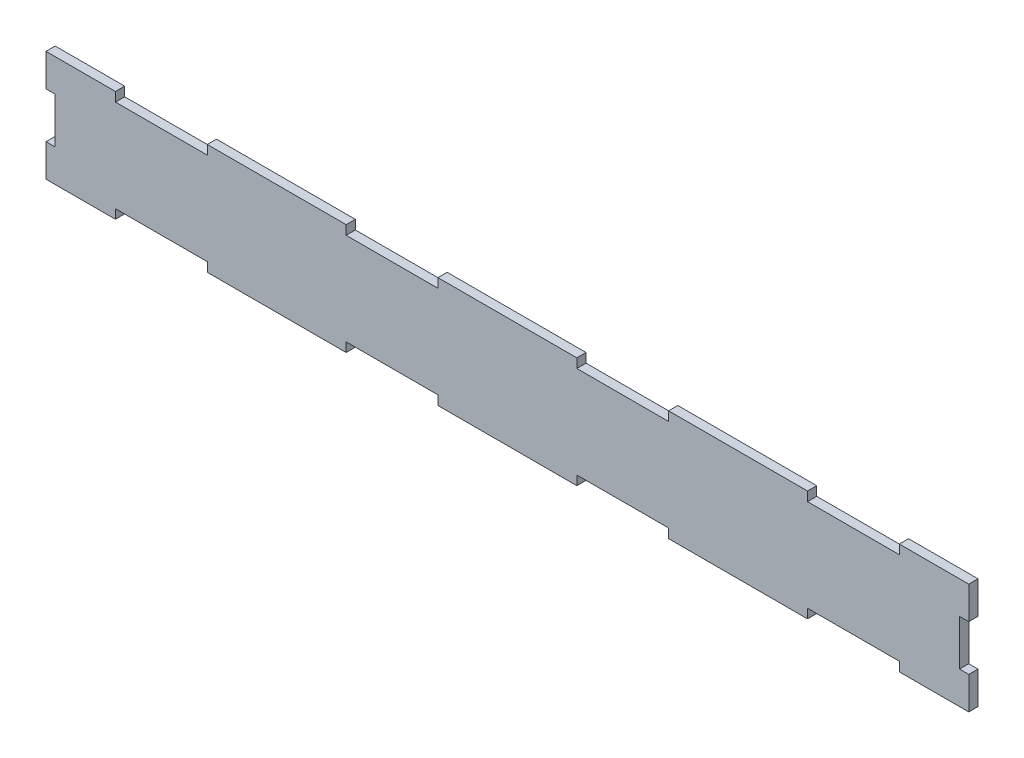
SolidWorks part; units mm, degrees
ref_plane "Front Plane" through (0, 0, 0) normal (0, 0, 1) x (1, 0, 0)
ref_plane "Top Plane" through (0, 0, 0) normal (0, 1, 0) x (1, 0, 0)
ref_plane "Right Plane" through (0, 0, 0) normal (1, 0, 0) x (0, 0, -1)
sketch "Sketch1" plane through (0, 0, 0) normal (0, 0, 1) x (1, 0, 0)
  line L0 (-392, -19.8) -> (-392, 19.8)
  line L1 (400, -48) -> (339.8, -48)
  line L2 (400, -48) -> (400, -19.8)
  line L3 (400, 48) -> (339.8, 48)
  line L4 (-400, -48) -> (-400, -19.8)
  line L5 (400, -48) -> (-400, 48) construction
  line L6 (400, 48) -> (-400, -48) construction
  line L7 (339.8, 40) -> (260.2, 40)
  line L8 (392, -19.8) -> (392, 19.8)
  line L9 (339.8, -40) -> (260.2, -40)
  line L10 (0, 0) -> (0, 150.7246) construction
  line L11 (-200, 171.805) -> (-200, -11.5942) construction
  line L12 (-300, 150.7246) -> (-300, -11.5942) construction
  line L13 (-339.8, 48) -> (-339.8, 40)
  line L14 (-260.2, 48) -> (-260.2, 40)
  line L15 (-139.8, 48) -> (-139.8, 40)
  line L16 (-60.2, 48) -> (-60.2, 40)
  line L17 (60.2, 48) -> (60.2, 40)
  line L18 (139.8, 48) -> (139.8, 40)
  line L19 (260.2, 48) -> (260.2, 40)
  line L20 (339.8, 48) -> (339.8, 40)
  line L21 (0, 0) -> (-499.1198, 0) construction
  line L22 (-400, 19.8) -> (-392, 19.8)
  line L23 (-400, -19.8) -> (-392, -19.8)
  line L24 (400, -19.8) -> (392, -19.8)
  line L25 (400, 19.8) -> (392, 19.8)
  line L26 (339.8, -48) -> (339.8, -40)
  line L27 (260.2, -48) -> (260.2, -40)
  line L28 (139.8, -48) -> (139.8, -40)
  line L29 (60.2, -48) -> (60.2, -40)
  line L30 (-60.2, -48) -> (-60.2, -40)
  line L31 (-139.8, -48) -> (-139.8, -40)
  line L32 (-260.2, -48) -> (-260.2, -40)
  line L33 (-339.8, -48) -> (-339.8, -40)
  line L34 (-339.8, 48) -> (-400, 48)
  line L35 (-260.2, 40) -> (-339.8, 40)
  line L36 (400, 48) -> (-400, 48) construction
  line L37 (392, 40) -> (-392, 40) construction
  line L38 (-392, -40) -> (-392, 40) construction
  line L39 (-60.2, 40) -> (-139.8, 40)
  line L40 (-139.8, 48) -> (-260.2, 48)
  line L41 (60.2, 48) -> (-60.2, 48)
  line L42 (139.8, 40) -> (60.2, 40)
  line L43 (260.2, 48) -> (139.8, 48)
  line L44 (400, 19.8) -> (400, 48)
  line L45 (392, -40) -> (392, 40) construction
  line L46 (260.2, -48) -> (139.8, -48)
  line L47 (400, -48) -> (400, 48) construction
  line L48 (392, -40) -> (-392, -40) construction
  line L49 (139.8, -40) -> (60.2, -40)
  line L50 (400, -48) -> (-400, -48) construction
  line L51 (60.2, -48) -> (-60.2, -48)
  line L52 (-60.2, -40) -> (-139.8, -40)
  line L53 (-139.8, -48) -> (-260.2, -48)
  line L54 (-260.2, -40) -> (-339.8, -40)
  line L55 (-339.8, -48) -> (-400, -48)
  line L56 (-400, 19.8) -> (-400, 48)
  line L58 (-400, -48) -> (-400, 48) construction
  point P0 (0, 0)
  point P18 (-339.8, 44)
  dimension "D1" = 800
  dimension "D2" = 96
  dimension "D4" = 200
  dimension "D5" = 100
  dimension "D6" = 39.8
  dimension "D7" = 19.8
  dimension "D3" = 8
extrude "Boss-Extrude1" add sketch "Sketch1" along normal blind 8
